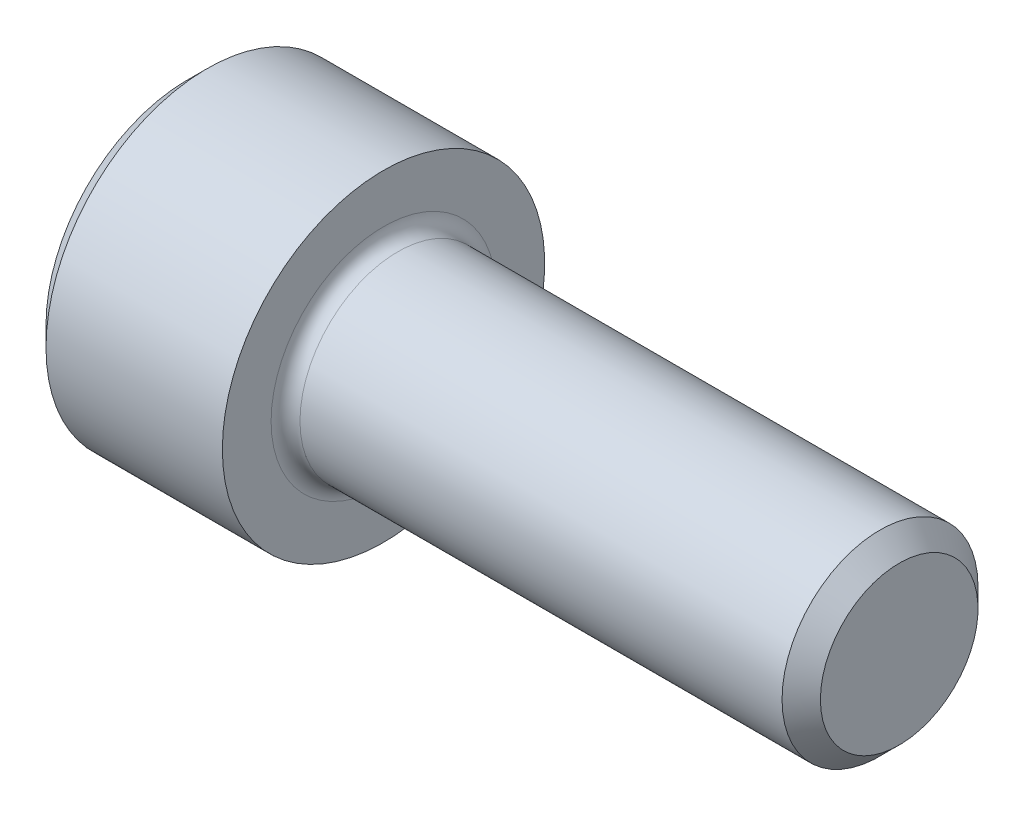
SolidWorks part; units mm, degrees
revolve "Base-Revolve" add sketch "BodySke"
sketch "BodySke" plane through (0, 0, 0) normal (0, 0, 1) x (1, 0, 0)
  line L0 (0, 0) -> (0, 3.4861)
  line L1 (0.4826, 3.9688) -> (4.826, 3.9688)
  line L2 (4.826, 3.9688) -> (4.826, 2.413)
  line L3 (4.826, 2.413) -> (17.0536, 2.413)
  line L4 (17.526, 1.9406) -> (17.526, 0)
  line L5 (17.526, 0) -> (0, 0)
  line L6 (-31.75, 0) -> (127, 0) construction
  line L7 (0, 3.4861) -> (0.4826, 3.9688)
  line L8 (17.526, 1.9406) -> (17.0536, 2.413)
  line L9 (0, -3.4861) -> (0.4826, -3.9688) construction
  line L10 (17.526, -1.9406) -> (17.0536, -2.413) construction
  line L11 (5.6185, 9.525) -> (5.6185, 3.175) construction
  line L12 (4.826, 9.525) -> (4.826, 3.175) construction
  line L13 (-20.574, 9.525) -> (-20.574, 3.175) construction
  dimension "Diameter" = 4.826
  dimension "Head_ht" = 4.826
  dimension "Length" = 12.7
  dimension "Body_ch_ang" = 45
  dimension "Head_dia" = 7.9375
  dimension "Head_ch_ang" = 45
  dimension "Head_side_ht" = 4.3434
  dimension "Minor_dia" = 3.8811
  dimension "Advance" = 0.7925
  dimension "Thread_nom" = 12.7
  dimension "Thread_length" = 38.1
cosmetic thread "ThreadCosmetic" [suppressed]
fillet "Fillet1" radius 0.3556 1 edges at (4.826, 0, 2.413)
ref_plane "Plane1" through (0, 0, 0) normal (0, 0, 1) x (1, 0, 0)
ref_plane "Plane2" through (0, 0, 0) normal (0, 1, 0) x (1, 0, 0)
ref_plane "Plane3" through (0, 0, 0) normal (1, 0, 0) x (0, 0, -1)
other "Configuration Table"
sketch "Sketch2" plane through (0, 0, 0) normal (0, 0, 1) x (1, 0, 0)
  line L0 (0, 1.985) -> (2.286, 1.985)
  line L1 (2.286, 1.985) -> (3.432, 0)
  line L2 (-31.75, 0) -> (127, 0) construction
  line L3 (3.432, 0) -> (0, 0)
  line L4 (0, 0) -> (0, 1.985)
  line L5 (0, 3.4861) -> (0, -3.4861) construction
  line L6 (0, 0) -> (47.625, 0) construction
  line L7 (4.826, -3.9688) -> (4.826, 3.9688) construction
  dimension "D1" = 1.985
  dimension "D2" = 60
revolve "Hex-PreBroach" cut sketch "Sketch2" angle 360 about L6
sketch "Sketch3" plane through (0, 0, 0) normal (-1, 0, 0) x (0, 0.5, 0.866)
  line L0 (1.146, 1.985) -> (-1.146, 1.985)
  line L1 (-1.146, 1.985) -> (-2.2921, 0)
  line L2 (1.146, 1.985) -> (2.2921, 0)
  line L3 (1.146, -1.985) -> (2.2921, 0)
  line L4 (1.146, -1.985) -> (-1.146, -1.985)
  line L5 (-1.146, -1.985) -> (-2.2921, 0)
  dimension "D1" = 1.985
  dimension "D2" = 1.985
  dimension "Hex_size" = 3.97
extrude "Hex" cut sketch "Sketch3" against normal blind 2.286
sketch "Sketch4" plane through (0, 0, 0) normal (-1, 0, 0) x (0, 0, 1)
  line L0 (0, 0) -> (2.3876, 0)
  line L1 (0, 0) -> (6.1484, 3.5498) construction
  line L2 (0, 0) -> (1.1938, 2.0677)
  line L3 (1.9883, 0.576) -> (2.2704, 0.7389)
  line L4 (1.493, 1.4339) -> (1.7751, 1.5968)
  arc A0 (1.9883, 0.576) -> (1.493, 1.4339) centre (0, 0) ccw
  arc A1 (2.3876, 0) -> (2.2704, 0.7389) centre (0, 0) ccw
  arc A2 (1.1938, 2.0677) -> (1.7751, 1.5968) centre (0, 0) cw
  dimension "D1" = 30
  dimension "D2" = 60
  dimension "Spline_p_dim" = 0.9906
  dimension "D3" = 0.4953
extrude "Spline" [suppressed] cut sketch "Sketch4" against normal blind 2.286
pattern_circular "CirPattern1" [suppressed] count 6 every 60
sketch "Sketch5" plane through (0, 0, 0) normal (0, 0, 1) x (1, 0, 0)
  line L0 (-31.75, 0) -> (127, 0) construction
  line L2 (0, 3.4861) -> (0, -3.4861) construction
  circle A0 centre (1.651, 0) radius 0.5905
  dimension "Drilled_hole_dia" = 1.1811
  dimension "Drilled_hole_loc" = 1.651
extrude "Hole" [suppressed] cut sketch "Sketch5" against normal through all and the other way through all
pattern_circular "Drilled-4" [suppressed] count 2 every 60
pattern_circular "Drilled-6" [suppressed] count 3 every 60
sketch "ThdSchSke" plane through (0, 0, 0) normal (0, 0, 1) x (1, 0, 0)
  line L0 (5.6185, -1.9406) -> (5.2877, -2.413)
  line L1 (5.6185, -1.9406) -> (5.9493, -2.413)
  line L2 (5.9493, -2.413) -> (5.9493, -3.0163)
  line L3 (-3.175, 0) -> (5.1513, 0) construction
  line L5 (5.9493, -3.0163) -> (5.2877, -3.0163)
  line L6 (5.2877, -3.0163) -> (5.2877, -2.413)
  line L7 (0, 3.4861) -> (0, -3.4861) construction
  dimension "Thread_minor" = 3.8811
  dimension "Diameter" = 4.826
  dimension "Start" = 5.6185
revolve "ThreadSchematic" [suppressed] cut sketch "ThdSchSke" angle 360 about L3
pattern_linear "ThdSchPat" [suppressed]
equation "\"D2@Sketch3\" = \"Hex_size@Sketch3\" / 2"
equation "\"D1@Sketch3\" = \"Hex_size@Sketch3\" / 2"
equation "\"D1@Sketch2\" = \"Hex_size@Sketch3\" / 2"
equation "\"D3@Sketch4\" = \"Spline_p_dim@Sketch4\" / 2"
equation "\"Thread_minor@ThreadCosmetic\"  =  \"Minor_dia@BodySke\""
equation "\"D2@CirPattern1\" = 360 / \"Num_teeth@CirPattern1\""
equation "\"Wall_thickness@Sketch2\" = \"Head_ht@BodySke\" - \"Key_eng@Hex\""
equation "\"Thread_length@ThreadCosmetic\" = ((sgn( (\"Length@BodySke\" - \"Advance@BodySke\" ) - \"Thread_nom@BodySke\" )-1)*( (\"Length@BodySke\" - \"Advance@BodySke\" ) - \"Thread_nom@BodySke\" ))/-2+ \"Thread_nom@BodySke\""
equation "\"Thread_minor@ThdSchSke\" = \"Minor_dia@BodySke\""
equation "\"Diameter@ThdSchSke\" = \"Diameter@BodySke\""
equation "\"Overcut@ThdSchSke\" = \"Diameter@BodySke\" * 1.25"
equation "\"Start@ThdSchSke\" = \"Head_ht@BodySke\" + \"Length@BodySke\" - \"Thread_length@ThreadCosmetic\"  '---Non-countersunk---"
equation "\"Num_threads@ThdSchPat\" = int( \"Thread_length@ThreadCosmetic\" / \"Advance@BodySke\" + 0.999 )  + 1"
equation "\"Advance@ThdSchPat\" = \"Thread_length@ThreadCosmetic\" /  (\"Num_threads@ThdSchPat\" - 1) 'relax it"
equation "\"Num_threads@ThdSchPat\" = \"Num_threads@ThdSchPat\" - sgn( \"Num_threads@ThdSchPat\" - 1) '---chamfered tips only---"
